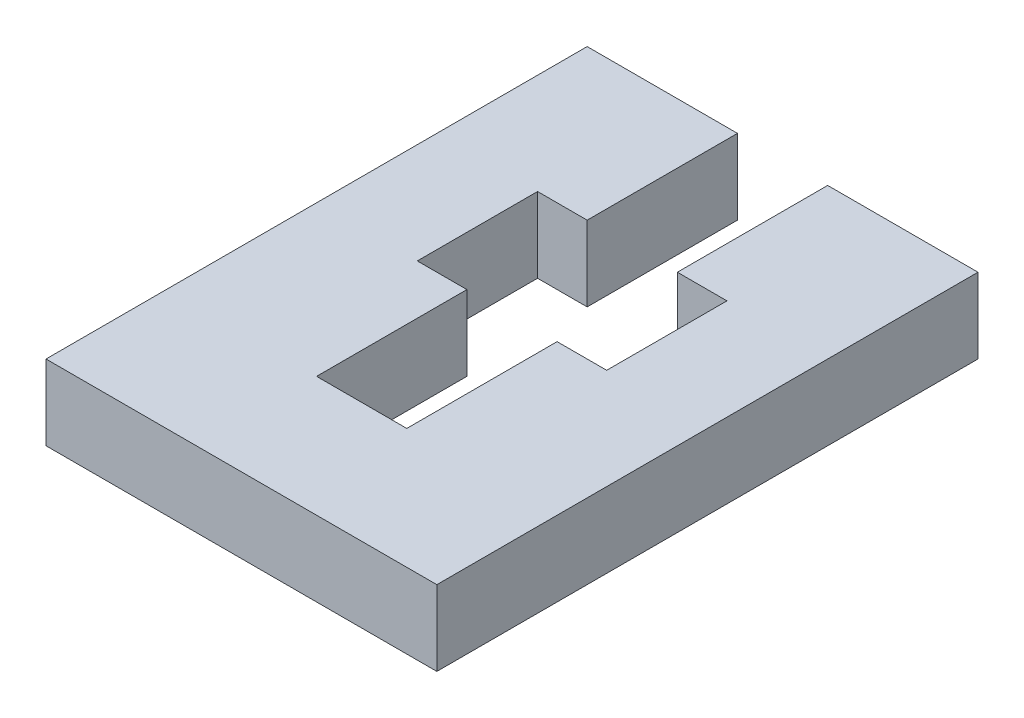
SolidWorks part; units mm, degrees
ref_plane "Front Plane" through (0, 0, 0) normal (0, 0, 1) x (1, 0, 0)
ref_plane "Top Plane" through (0, 0, 0) normal (0, 1, 0) x (1, 0, 0)
ref_plane "Right Plane" through (0, 0, 0) normal (1, 0, 0) x (0, 0, -1)
sketch "Sketch1" plane through (0, 0, 0) normal (0, 1, 0) x (1, 0, 0)
  line L0 (1.5, 8.5) -> (1.5, 3.5)
  line L1 (1.5, 3.5) -> (3.15, 3.5)
  line L2 (3.15, 3.5) -> (3.15, -0.5)
  line L3 (3.15, -0.5) -> (1.5, -0.5)
  line L4 (1.5, -0.5) -> (1.5, -5.5)
  line L5 (1.5, -5.5) -> (-1.5, -5.5)
  line L6 (-1.5, -5.5) -> (-1.5, -0.5)
  line L7 (-1.5, -0.5) -> (-3.15, -0.5)
  line L8 (-3.15, -0.5) -> (-3.15, 3.5)
  line L9 (-3.15, 3.5) -> (-1.5, 3.5)
  line L10 (-1.5, 3.5) -> (-1.5, 8.5)
  line L12 (-1.5, 8.5) -> (-6.5, 8.5)
  line L13 (-6.5, 8.5) -> (-6.5, -9.5)
  line L14 (-6.5, -9.5) -> (6.5, -9.5)
  line L15 (6.5, -9.5) -> (6.5, 8.5)
  line L16 (6.5, 8.5) -> (1.5, 8.5)
  point P0 (0, -5.5)
  point P17 (0, -9.5)
  dimension "D1" = 5
  dimension "D2" = 4
  dimension "D3" = 1.65
  dimension "D4" = 1.65
  dimension "D5" = 5
  dimension "D6" = 3
  dimension "D7" = 5
  dimension "D8" = 4
extrude "Boss-Extrude1" add sketch "Sketch1" along normal blind 2.5
